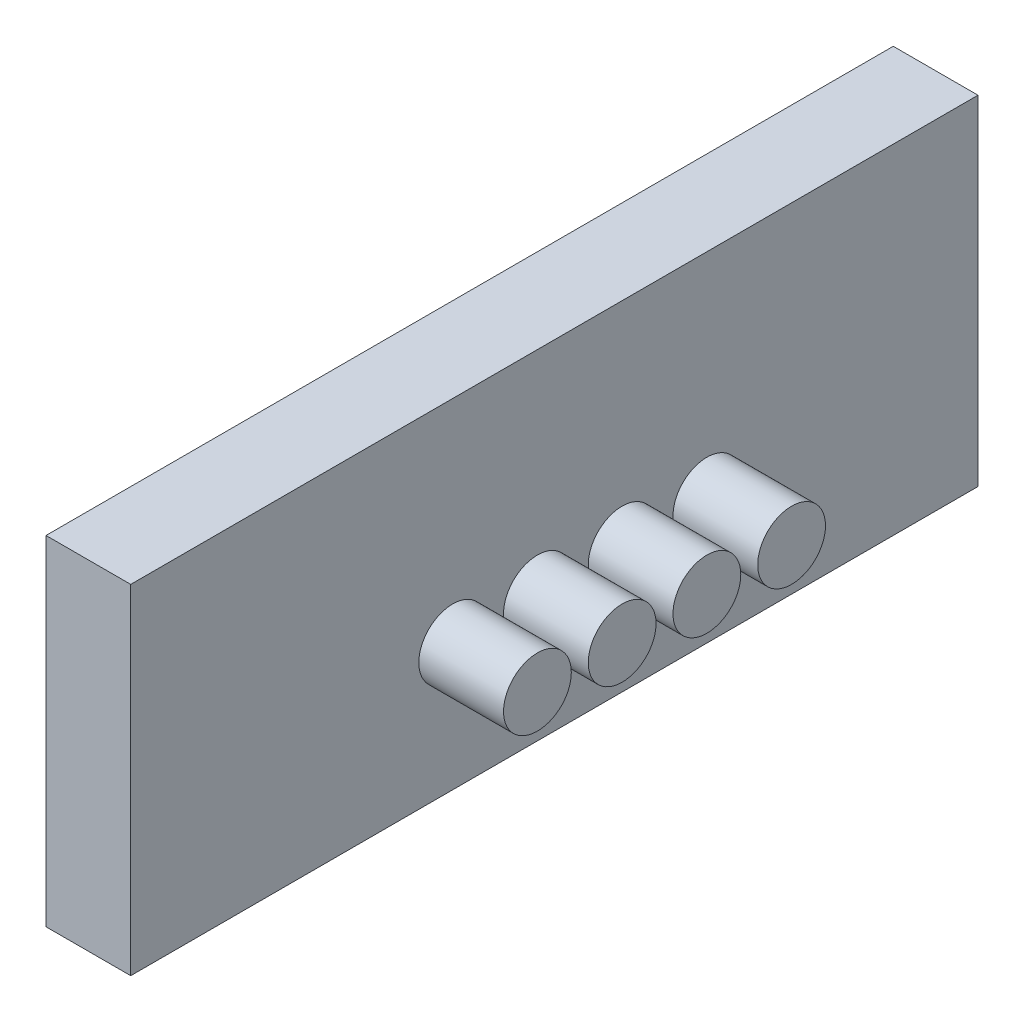
SolidWorks part; units mm, degrees
ref_plane "Front Plane" through (0, 0, 0) normal (0, 0, 1) x (1, 0, 0)
ref_plane "Top Plane" through (0, 0, 0) normal (0, 1, 0) x (1, 0, 0)
ref_plane "Right Plane" through (0, 0, 0) normal (1, 0, 0) x (0, 0, -1)
sketch "Sketch1" plane through (0, 0, 0) normal (1, 0, 0) x (0, 0, -1)
  line L1 (50, -20) -> (-50, -20)
  line L2 (50, -20) -> (50, 20)
  line L3 (50, 20) -> (-50, 20)
  line L4 (-50, -20) -> (-50, 20)
  line L5 (50, -20) -> (-50, 20) construction
  line L6 (50, 20) -> (-50, -20) construction
  point P0 (0, 0)
  dimension "manifold_length" = 100
  dimension "manifold_width" = 40
extrude "Boss-Extrude1" add sketch "Sketch1" along normal blind 10
sketch "Sketch2" plane through (10, 0, 0) normal (1, 0, 0) x (0, 0, -1)
  line L0 (50, 20) -> (-50, 20) construction
  line L1 (50, -20) -> (50, 20) construction
  circle A0 centre (18, -5) radius 4
  circle A1 centre (8, -5) radius 4
  circle A2 centre (-2, -5) radius 4
  circle A3 centre (-12, -5) radius 4
  dimension "D1" = 8
  dimension "D2" = 8
  dimension "D3" = 8
  dimension "D4" = 8
  dimension "D5" = 10
  dimension "D6" = 10
  dimension "D7" = 10
  dimension "y1" = 25
  dimension "y2" = 25
  dimension "y3" = 25
  dimension "y4" = 25
  dimension "x1" = 32
extrude "Boss-Extrude2" add sketch "Sketch2" along normal blind 10
sketch "Sketch3" plane through (0, 0, 0) normal (-1, 0, 0) x (0, 0, 1)
  line L0 (-50, -20) -> (-50, 20) construction
  line L1 (-50, 20) -> (50, 20) construction
  circle A0 centre (0, 0) radius 7.5
  dimension "D1" = 15
  dimension "D2" = 50
  dimension "D3" = 20
split line "Split Line1"
equation "\"in_manifold_dia\"= 15 '1"
equation "\"tube_diameter1\"= 8'4"
equation "\"z_td1\"= \"side_edge_2_tube1\""
equation "\"y_td1\"= \"top_edge_2_tube\""
equation "\"tube_diameter2\"= 8'5"
equation "\"y_td2\"= \"top_edge_2_tube\""
equation "\"tube_diameter3\"= 8'6"
equation "\"y_td3\"= \"top_edge_2_tube\""
equation "\"tube_diameter4\"= 8'7"
equation "\"y_td4\"= \"top_edge_2_tube\""
equation "\"tube_distance\"= 10'if d=8 and s2e1=5, min=8.5, max =30"
equation "\"D1@Sketch2\" = \"tube_diameter1\""
equation "\"D2@Sketch2\"= \"tube_diameter2\""
equation "\"D3@Sketch2\" = \"tube_diameter3\""
equation "\"D4@Sketch2\" = \"tube_diameter4\""
equation "\"manifold_length@Sketch1\" = 100"
equation "\"manifold_width@Sketch1\" = 40"
equation "\"D5@Sketch2\" = \"tube_distance\""
equation "\"y1@Sketch2\"= \"y_td1\""
equation "\"side_edge_2_tube1\"= 32'for l=100, d=10 (varies 8.5 to 30), max=65, min=d/2+1"
equation "\"x1@Sketch2\" = \"z_td1\"'shifting one, shifts all!"
equation "\"top_edge_2_tube\"= 25'd/2+1  to width-(d/2+1)"
equation "\"D1@Sketch3\"=\"in_manifold_dia\""
equation "\"D2@Sketch3\"= 50'inlet circle distance from edge"
equation "\"D3@Sketch3\"= 20'inlet circle distance form top edge"
equation "\"y2@Sketch2\"= \"y_td2\""
equation "\"y3@Sketch2\"= \"y_td3\""
equation "\"y4@Sketch2\"= \"y_td4\""
equation "\"D6@Sketch2\"= \"tube_distance\""
equation "\"D7@Sketch2\"= \"tube_distance\""
